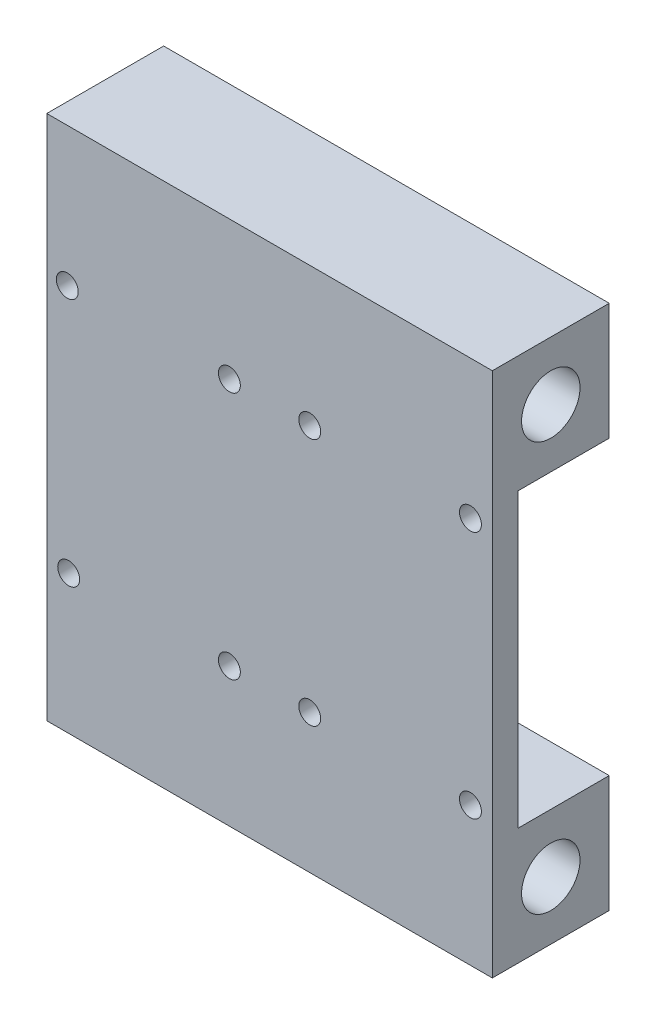
SolidWorks part; units mm, degrees
ref_plane "Front Plane" through (0, 0, 0) normal (0, 0, 1) x (1, 0, 0)
ref_plane "Top Plane" through (0, 0, 0) normal (0, 1, 0) x (1, 0, 0)
ref_plane "Right Plane" through (0, 0, 0) normal (1, 0, 0) x (0, 0, -1)
sketch "Sketch1" plane through (0, 0, 0) normal (0, 0, 1) x (1, 0, 0)
  line L0 (0, 0) -> (0, 40)
  line L1 (0, 40) -> (115, 40)
  line L2 (115, 40) -> (115, 0)
  line L4 (110, 34) -> (110, 6) construction
  line L5 (0, 0) -> (5, 0)
  line L6 (5, 0) -> (55, 0)
  line L7 (60, 0) -> (110, 0)
  line L8 (110, 0) -> (115, 0)
  line L9 (5, 34) -> (5, 40) construction
  line L10 (55, 0) -> (60, 0)
  line L11 (5, 40) -> (11, 34) construction
  line L12 (11, 34) -> (5, 34) construction
  line L13 (5, 0) -> (5, 6) construction
  line L14 (5, 6) -> (11, 6) construction
  line L15 (5, 34) -> (5, 6) construction
  line L16 (5, 0) -> (11, 6) construction
  line L17 (110, 40) -> (104, 34) construction
  line L18 (104, 34) -> (110, 34) construction
  line L19 (110, 34) -> (110, 40) construction
  line L20 (110, 0) -> (104, 6) construction
  line L21 (104, 6) -> (110, 6) construction
  line L22 (110, 6) -> (110, 0) construction
  line L26 (60, 0) -> (60, 40) construction
  line L27 (55, 40) -> (49, 34) construction
  line L28 (55, 0) -> (55, 40) construction
  line L29 (49, 34) -> (55, 34) construction
  line L30 (60, 40) -> (66, 34) construction
  line L31 (66, 34) -> (60, 34) construction
  line L32 (55, 0) -> (49, 6) construction
  line L33 (49, 6) -> (55, 6) construction
  line L34 (60, 0) -> (66, 6) construction
  line L35 (66, 6) -> (60, 6) construction
  point P26 (107, 37)
  point P35 (107, 3)
  point P36 (63, 3)
  point P37 (63, 37)
  point P38 (52, 37)
  point P39 (52, 3)
  point P40 (8, 3)
  point P41 (8, 37)
  dimension "D5" = 6
  dimension "D1" = 115
  dimension "D2" = 40
  dimension "D3" = 5
extrude "Boss-Extrude1" add sketch "Sketch1" along normal blind 3.5
sketch "Sketch5" plane through (115, 0, 0) normal (1, 0, 0) x (0, 0, -1)
  line L0 (-3.5, 40) -> (12.5, 40)
  line L3 (-3.5, 0) -> (12.5, 0)
  line L4 (4.5, 56) -> (4.5, 40) construction
  line L6 (-3.5, 40) -> (-3.5, 56)
  line L7 (-3.5, 56) -> (12.5, 56)
  line L8 (12.5, 56) -> (12.5, 40)
  line L12 (12.5, 0) -> (12.5, -16)
  line L13 (12.5, -16) -> (-3.5, -16)
  line L14 (-3.5, -16) -> (-3.5, 0)
  line L15 (4.5, 0) -> (4.5, -16) construction
  circle A0 centre (4.5, -8) radius 4
  circle A1 centre (4.5, 48) radius 4
  dimension "D2" = 8
  dimension "D1" = 16
extrude "Boss-Extrude2" add sketch "Sketch5" against normal up to surface (115 mm away) up to face at (0, 20, 1.75)
sketch "Sketch8" plane through (0, 0, 0) normal (0, 0, -1) x (-1, 0, 0)
  line L0 (-107, 37) -> (-63, 37) construction
  line L1 (-60, 0) -> (-66, 6) construction
  line L2 (-55, 0) -> (-49, 6) construction
  line L4 (-52, 37) -> (-7.6194, 37) construction
  line L6 (-8, 3) -> (-52, 3) construction
  line L8 (-63, 3) -> (-107, 3) construction
  circle A0 centre (-107, 37) radius 1.5
  circle A1 centre (-63, 37) radius 1.5
  circle A2 centre (-52, 37) radius 1.5
  circle A3 centre (-8, 37) radius 1.5
  circle A4 centre (-8, 3) radius 1.5
  circle A6 centre (-63, 3) radius 1.5
  circle A7 centre (-52, 3) radius 1.5
  circle A8 centre (-107, 3) radius 1.5
  circle A9 centre (-85, 37) radius 1.5
  circle A10 centre (-29.8097, 37) radius 1.5
  circle A11 centre (-30, 3) radius 1.5
  circle A12 centre (-85, 3) radius 1.5
  dimension "D1" = 3
extrude "Cut-Extrude1" cut sketch "Sketch8" against normal up to surface (3.5 mm away) up to face at (57.5, 20, 3.5)
sketch "Sketch10" plane through (0, 0, -12.5) normal (0, 0, -1) x (-1, 0, 0)
  line L1 (-88, 56) -> (-88, 37)
  line L3 (0, 56) -> (-115, 56) construction
  line L4 (-88, 56) -> (-115, 56)
  line L5 (-115, 56) -> (-115, -16)
  line L6 (-115, -16) -> (-88, -16)
  line L7 (0, -16) -> (-115, -16) construction
  line L10 (-27, 56) -> (0, 56)
  line L11 (0, 56) -> (0, 40) construction
  line L12 (0, 56) -> (0, -16)
  line L13 (0, -16) -> (-27, -16)
  line L15 (-85, 37) -> (-88, 37) construction
  line L16 (-29.8097, 38.5) -> (-29.8097, 35.5) construction
  line L17 (-30, 37.0558) -> (-27, 37.0558) construction
  line L18 (-27, 37.0558) -> (-27, 56)
  line L19 (-27, 37.0558) -> (-27, -16)
  line L20 (-88, 37) -> (-88, -16)
  circle A1 centre (-29.8097, 37) radius 1.5 construction
  dimension "D1" = 3
extrude "Cut-Extrude2" cut sketch "Sketch10" against normal up to surface (16 mm away) up to face at (83.5, 37, 3.5)
equation "\"board_length\"= 260mm"
equation "\"board_height\"= 200mm"
equation "\"board_width\"= 16.5mm"
equation "\"token_thickness\"= 7mm"
equation "\"token_diameter\"= 32mm"
equation "\"board_side_lower_height\"= 55mm"
equation "\"board_side_height\"= 156.5mm"
equation "\"board_side_length\"= 100mm"
equation "\"board_slot_width\"= \"board_length\" / 7"
equation "\"token_ridge\"= ( \"token_thickness\" - 4mm ) / 2"
equation "\"token_ridge_width\"= 1.5mm"
equation "\"25T_outer_diameter\"= 20mm"
equation "\"25T_inner_diameter\"= 9mm"
equation "\"2T_screw_distance\"= 14mm"
equation "\"2T_outer_thickness\"= 2mm"
equation "\"2T_inner_thickness\"= 4.5mm"
equation "\"MG996R_outer_length\"= 54mm"
equation "\"MG996R_inner_length\"= 40mm"
equation "\"MG996R_width\"= 20mm"
equation "\"MG996R_height\"= 26.6mm"
equation "\"MG996R_full_height\"= 45.7mm"
equation "\"MG996R_full_width\"= 55.5mm"
equation "\"MG996R_screw_distance\"= 10mm"
equation "\"magnet_diameter\"= 10mm"
equation "\"magnet_thickness\"= 2mm"
equation "\"dispenser_barrel_margin\"= 2.5mm"
equation "\"dispenser_wheel_width\"= \"token_thickness\" + 5mm"
equation "\"dispenser_cover_margin\"= 3.0mm"
equation "\"dispenser_cover_thickness\"= 5.0mm"
equation "\"MG996R_major_axis_distance\"= 34.3mm"
equation "\"MG996R_major_screw_distance\"= 48.6mm"
equation "\"MG996R_minor_screw_distance\"= 9.9mm"
equation "\"MG996R_mid_height\"= 37.5mm"
equation "\"dispenser_slope\"= 30deg"
equation "\"dispenser_cover_length\"= 16mm"
equation "\"dispenser_carrier_width\"= 3.5mm"
equation "\"dispenser_carrier_height\"= 40mm"
equation "\"carrier_width\"= \"shaft_diameter\" * 2"
equation "\"shaft_diameter\"= 8mm"
equation "\"carrier_thickness\"=16"
equation "\"D1@Boss-Extrude1\"=\"dispenser_carrier_width\""
equation "\"D1@Sketch1\"=\"MG996R_outer_length\"*2+\"dispenser_cover_margin\"+4mm"
equation "\"D2@Sketch1\"=\"dispenser_carrier_height\""
equation "\"D3@Sketch1\"=\"dispenser_cover_thickness\""
equation "\"D1@Sketch5\"=\"carrier_width\""
equation "\"D2@Sketch5\"=\"shaft_diameter\""
equation "\"GT2_width\"= 7mm"
equation "\"GT2_outer_diameter\"= 18mm"
equation "\"GT2_inner_diameter\"= 12mm"
equation "\"GT2_pitch_diameter\"= 2mm"
equation "\"GT2_tooth_height\"= 1.6mm"
equation "\"GT2_upper_length\"= 0.4mm"
